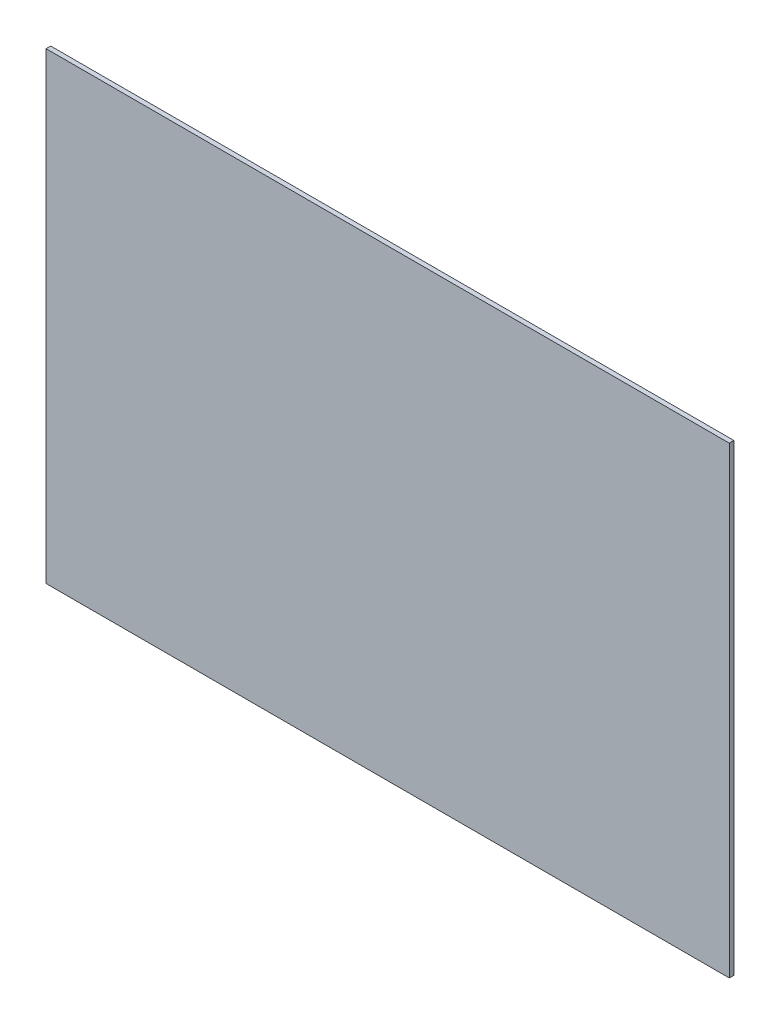
SolidWorks part; units mm, degrees
ref_plane "Front Plane" through (0, 0, 0) normal (0, 0, 1) x (1, 0, 0)
ref_plane "Top Plane" through (0, 0, 0) normal (0, 1, 0) x (1, 0, 0)
ref_plane "Right Plane" through (0, 0, 0) normal (1, 0, 0) x (0, 0, -1)
sketch "Sketch1" plane through (0, 0, 0) normal (0, 0, 1) x (1, 0, 0)
  line L1 (0, 0) -> (295, 0)
  line L2 (0, 0) -> (0, 200)
  line L3 (0, 200) -> (295, 200)
  line L4 (295, 0) -> (295, 200)
  dimension "D1" = 200
  dimension "D2" = 295
extrude "Boss-Extrude1" add sketch "Sketch1" along normal blind 2
